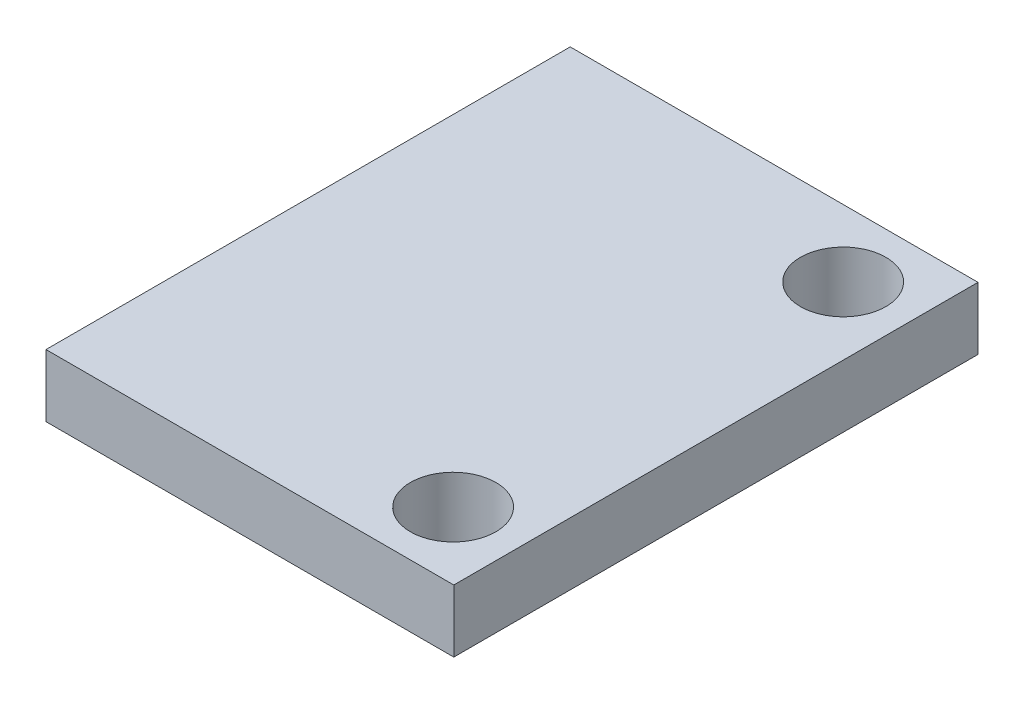
SolidWorks part; units mm, degrees
ref_plane "Front Plane" through (0, 0, 0) normal (0, 0, 1) x (1, 0, 0)
ref_plane "Top Plane" through (0, 0, 0) normal (0, 1, 0) x (1, 0, 0)
ref_plane "Right Plane" through (0, 0, 0) normal (1, 0, 0) x (0, 0, -1)
sketch "Sketch1" plane through (0, 0, 0) normal (0, 1, 0) x (1, 0, 0)
  line L0 (5.2578, 9.1821) -> (5.2578, 10.1219) construction
  line L1 (-7.874, -10.1219) -> (7.874, -10.1219)
  line L2 (-7.874, -10.1219) -> (-7.874, 10.1219)
  line L3 (-7.874, 10.1219) -> (7.874, 10.1219)
  line L4 (7.874, -10.1219) -> (7.874, 10.1219)
  line L5 (-7.874, -10.1219) -> (7.874, 10.1219) construction
  line L6 (-7.874, 10.1219) -> (7.874, -10.1219) construction
  line L7 (5.2578, -9.1821) -> (5.2578, -10.1219) construction
  circle A0 centre (5.2578, 7.5311) radius 1.651
  circle A1 centre (5.2578, -7.5311) radius 1.651
  point P0 (0, 0)
  point P10 (6.9088, 7.5311)
  point P12 (5.2578, 9.1821)
  point P14 (5.2578, -9.1821)
  point P18 (5.2578, 7.5311)
  point P19 (5.2578, -7.5311)
  dimension "D3" = 3.302
  dimension "D5" = 15.0622
  dimension "D1" = 20.2438
  dimension "D2" = 15.748
  dimension "D4" = 0.9652
extrude "Boss-Extrude1" add sketch "Sketch1" along normal blind 2.413
